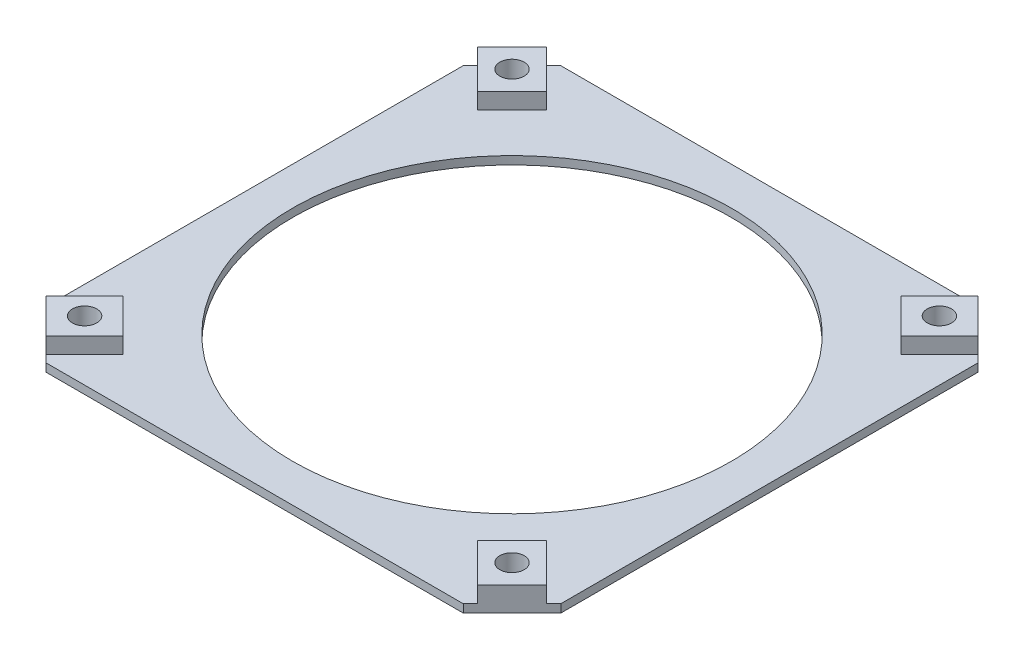
SolidWorks part; units mm, degrees
ref_plane "Front Plane" through (0, 0, 0) normal (0, 0, 1) x (1, 0, 0)
ref_plane "Top Plane" through (0, 0, 0) normal (0, 1, 0) x (1, 0, 0)
ref_plane "Right Plane" through (0, 0, 0) normal (1, 0, 0) x (0, 0, -1)
sketch "Sketch1" plane through (0, 0, 0) normal (0, 1, 0) x (1, 0, 0)
  line L0 (-31.68, 25.6768) -> (-25.68, 31.6768)
  line L1 (-25.68, -31.6768) -> (25.68, -31.6768)
  line L2 (-31.68, -25.6768) -> (-31.68, 25.6768)
  line L3 (-25.68, 31.6768) -> (25.68, 31.6768)
  line L4 (31.68, -25.6768) -> (31.68, 25.6768)
  line L5 (-31.68, -31.6768) -> (31.68, 31.6768) construction
  line L6 (-31.68, 31.6768) -> (31.68, -31.6768) construction
  line L7 (25.68, 31.6768) -> (31.68, 25.6768)
  line L8 (25.68, -31.6768) -> (31.68, -25.6768)
  line L9 (-31.68, -25.6768) -> (-25.68, -31.6768)
  circle A0 centre (0, 0) radius 27
  point P0 (0, 0)
  dimension "D2" = 54
  dimension "D1" = 63.36
  dimension "D3" = 89.6
extrude "Boss-Extrude1" add sketch "Sketch1" along normal blind 1
sketch "Sketch2" plane through (0, 1, 0) normal (0, 1, 0) x (1, 0, 0)
  line L0 (0, 0) -> (26.3044, 26.3044) construction
  line L1 (31.68, -25.6768) -> (31.68, 25.6768) construction
  line L6 (26.5571, 30.7997) -> (21.809, 26.0517)
  line L7 (26.5571, 30.7997) -> (30.7997, 26.5571)
  line L8 (31.68, 25.6768) -> (25.68, 31.6768) construction
  line L21 (21.809, 26.0517) -> (26.0517, 21.809)
  line L22 (-25.68, 31.6768) -> (-31.68, 25.6768) construction
  line L23 (-31.68, -25.6768) -> (-25.68, -31.6768) construction
  line L24 (30.7997, 26.5571) -> (26.0517, 21.809)
  line L25 (26.5571, 30.7997) -> (26.0517, 21.809) construction
  line L26 (21.809, 26.0517) -> (30.7997, 26.5571) construction
  line L27 (30.7997, -26.5571) -> (26.0517, -21.809)
  line L28 (30.7997, -26.5571) -> (26.5571, -30.7997)
  line L29 (26.5571, -30.7997) -> (21.809, -26.0517)
  line L30 (26.0517, -21.809) -> (21.809, -26.0517)
  line L31 (-26.5571, -30.7997) -> (-21.809, -26.0517)
  line L32 (-26.5571, -30.7997) -> (-30.7997, -26.5571)
  line L33 (-30.7997, -26.5571) -> (-26.0517, -21.809)
  line L34 (-21.809, -26.0517) -> (-26.0517, -21.809)
  line L35 (-30.7997, 26.5571) -> (-26.0517, 21.809)
  line L36 (-30.7997, 26.5571) -> (-26.5571, 30.7997)
  line L37 (-26.5571, 30.7997) -> (-21.809, 26.0517)
  line L38 (-26.0517, 21.809) -> (-21.809, 26.0517)
  point P12 (0, 0)
  point P25 (0, 0)
  point P26 (0, 0)
  point P27 (0, 0)
  dimension "D1" = 37.2
  dimension "D2" = 45
  dimension "D3" = 6
  dimension "D4" = 4
extrude "Boss-Extrude3" add sketch "Sketch2" along normal blind 2
sketch "Sketch14" plane through (0, 3, 0) normal (0, 1, 0) x (1, 0, 0)
  circle A0 centre (26.3044, 26.3044) radius 1.5
  dimension "D1" = 3
extrude "Cut-Extrude2" cut sketch "Sketch14" against normal through all
pattern_circular "CirPattern2" count 4 over 360 about axis through (0, 0, 0) along (0, 1, 0) of "Cut-Extrude2"
